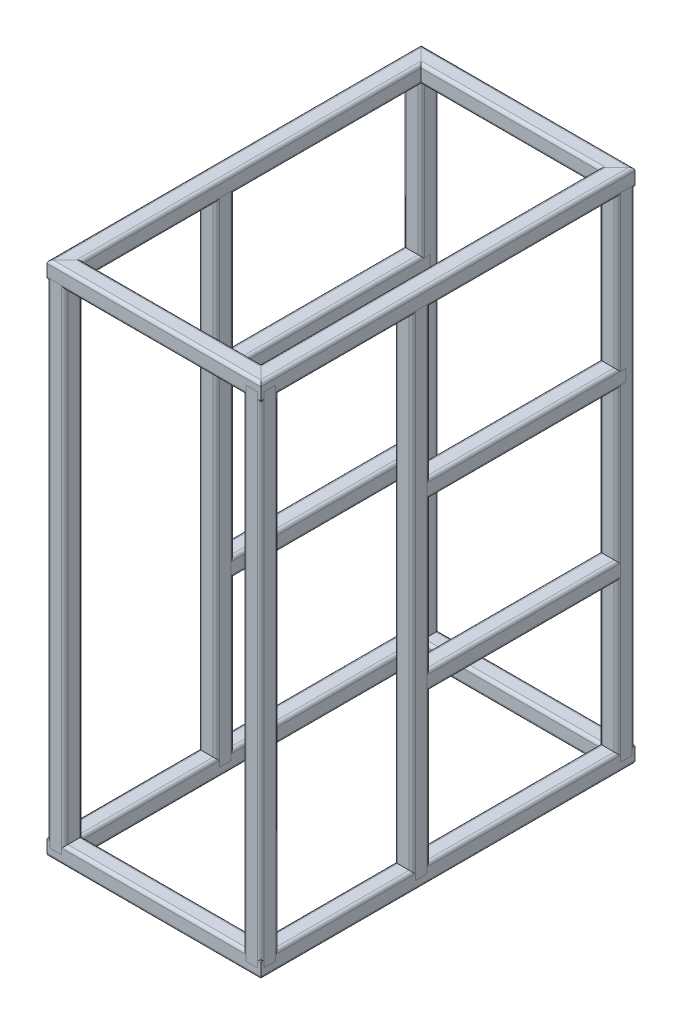
SolidWorks part; units mm, degrees
ref_plane "前视基准面" through (0, 0, 0) normal (0, 0, 1) x (1, 0, 0)
ref_plane "上视基准面" through (0, 0, 0) normal (0, 1, 0) x (1, 0, 0)
ref_plane "右视基准面" through (0, 0, 0) normal (1, 0, 0) x (0, 0, -1)
sketch "草图1" plane through (0, 0, 0) normal (0, 0, 1) x (1, 0, 0)
  line L1 (-165, -420) -> (165, -420)
  line L2 (-165, -420) -> (-165, 420)
  line L3 (-165, 420) -> (165, 420)
  line L4 (165, -420) -> (165, 420)
  line L5 (-165, -420) -> (165, 420) construction
  line L6 (-165, 420) -> (165, -420) construction
  point P0 (0, 0)
  dimension "D1" = 840
  dimension "D2" = 330
sketch3d "3D草图1"
  line L0 (165, 420, 0) -> (165, 420, -600)
  line L1 (165, 420, -600) -> (165, -420, -600)
  line L2 (165, -420, 0) -> (165, -420, -600)
  line L3 (-165, 420, 0) -> (-165, 420, -600)
  line L4 (-165, 420, -600) -> (165, 420, -600)
  line L5 (-165, 420, -600) -> (-165, -420, -600)
  line L6 (-165, -420, 0) -> (-165, -420, -600)
  line L7 (165, -420, -600) -> (-165, -420, -600)
  line L8 (165, -420, -255) -> (165, 420, -255)
  line L9 (-165, -420, -255) -> (-165, 420, -255)
  line L10 (165, -140, -255) -> (165, -140, -600)
  line L11 (165, 140, -255) -> (165, 140, -600)
  line L12 (-165, 140, -255) -> (-165, 140, -600)
  line L13 (-165, -140, -255) -> (-165, -140, -600)
  line L14 (165, -420, 0) -> (165, 420, 0) construction
  line L15 (-165, -420, 0) -> (-165, 420, 0) construction
  dimension "D1" = 280
  dimension "D2" = 280
  dimension "D3" = 255
  dimension "D4" = 280
  dimension "D5" = 280
  dimension "D6" = 255
  dimension "D7" = 600
other "方形管 30 X 30 X 2.6(1)"
ref_plane "基准面1" through (-165, -420, 0) normal (1, 0, 0) x (0, 1, 0)
sketch "Sketch1" plane through (-165, -420, 0) normal (1, 0, 0) x (0, 1, 0)
  line L0 (-9.8, -12.4) -> (9.8, -12.4)
  line L1 (-12.4, -9.8) -> (-12.4, 9.8)
  line L2 (9.8, 12.4) -> (-9.8, 12.4)
  line L3 (12.4, 9.8) -> (12.4, -9.8)
  line L4 (-9.8, -15) -> (9.8, -15)
  line L5 (-15, -9.8) -> (-15, 9.8)
  line L6 (9.8, 15) -> (-9.8, 15)
  line L7 (15, 9.8) -> (15, -9.8)
  arc A0 (15, 9.8) -> (9.8, 15) centre (9.8, 9.8) ccw
  arc A1 (9.8, -15) -> (15, -9.8) centre (9.8, -9.8) ccw
  arc A2 (-15, -9.8) -> (-9.8, -15) centre (-9.8, -9.8) ccw
  arc A3 (-9.8, 15) -> (-15, 9.8) centre (-9.8, 9.8) ccw
  arc A4 (-9.8, 12.4) -> (-12.4, 9.8) centre (-9.8, 9.8) ccw
  arc A5 (12.4, 9.8) -> (9.8, 12.4) centre (9.8, 9.8) ccw
  arc A6 (9.8, -12.4) -> (12.4, -9.8) centre (9.8, -9.8) ccw
  arc A7 (-12.4, -9.8) -> (-9.8, -12.4) centre (-9.8, -9.8) ccw
  point P0 (-15, 0)
  point P1 (15, 0)
  point P2 (0, 15)
  point P3 (0, -15)
  point P4 (0, 0)
  point P5 (-15, -15)
  point P6 (15, -15)
  point P7 (15, 15)
  point P8 (-15, 15)
  point P33 (0, 0)
  dimension "D1" = 5.2
  dimension "Thickness" = 2.6
  dimension "V_leg" = 30
other "方形管 30 X 30 X 2.6(2)"
ref_plane "基准面2" through (165, -420, 0) normal (0, 1, 0) x (-1, 0, 0)
sketch "Sketch11" plane through (165, -420, 0) normal (0, 1, 0) x (-1, 0, 0)
  line L0 (-9.8, -12.4) -> (9.8, -12.4)
  line L1 (-12.4, -9.8) -> (-12.4, 9.8)
  line L2 (9.8, 12.4) -> (-9.8, 12.4)
  line L3 (12.4, 9.8) -> (12.4, -9.8)
  line L4 (-9.8, -15) -> (9.8, -15)
  line L5 (-15, -9.8) -> (-15, 9.8)
  line L6 (9.8, 15) -> (-9.8, 15)
  line L7 (15, 9.8) -> (15, -9.8)
  arc A0 (15, 9.8) -> (9.8, 15) centre (9.8, 9.8) ccw
  arc A1 (9.8, -15) -> (15, -9.8) centre (9.8, -9.8) ccw
  arc A2 (-15, -9.8) -> (-9.8, -15) centre (-9.8, -9.8) ccw
  arc A3 (-9.8, 15) -> (-15, 9.8) centre (-9.8, 9.8) ccw
  arc A4 (-9.8, 12.4) -> (-12.4, 9.8) centre (-9.8, 9.8) ccw
  arc A5 (12.4, 9.8) -> (9.8, 12.4) centre (9.8, 9.8) ccw
  arc A6 (9.8, -12.4) -> (12.4, -9.8) centre (9.8, -9.8) ccw
  arc A7 (-12.4, -9.8) -> (-9.8, -12.4) centre (-9.8, -9.8) ccw
  point P0 (-15, 0)
  point P1 (15, 0)
  point P2 (0, 15)
  point P3 (0, -15)
  point P4 (0, 0)
  point P5 (-15, -15)
  point P6 (15, -15)
  point P7 (15, 15)
  point P8 (-15, 15)
  point P33 (0, 0)
  dimension "D1" = 5.2
  dimension "Thickness" = 2.6
  dimension "V_leg" = 30
other "方形管 30 X 30 X 2.6(4)"
ref_plane "基准面3" through (-165, 420, 0) normal (1, 0, 0) x (0, 1, 0)
sketch "Sketch12" plane through (-165, 420, 0) normal (1, 0, 0) x (0, 1, 0)
  line L0 (-9.8, -12.4) -> (9.8, -12.4)
  line L1 (-12.4, -9.8) -> (-12.4, 9.8)
  line L2 (9.8, 12.4) -> (-9.8, 12.4)
  line L3 (12.4, 9.8) -> (12.4, -9.8)
  line L4 (-9.8, -15) -> (9.8, -15)
  line L5 (-15, -9.8) -> (-15, 9.8)
  line L6 (9.8, 15) -> (-9.8, 15)
  line L7 (15, 9.8) -> (15, -9.8)
  arc A0 (15, 9.8) -> (9.8, 15) centre (9.8, 9.8) ccw
  arc A1 (9.8, -15) -> (15, -9.8) centre (9.8, -9.8) ccw
  arc A2 (-15, -9.8) -> (-9.8, -15) centre (-9.8, -9.8) ccw
  arc A3 (-9.8, 15) -> (-15, 9.8) centre (-9.8, 9.8) ccw
  arc A4 (-9.8, 12.4) -> (-12.4, 9.8) centre (-9.8, 9.8) ccw
  arc A5 (12.4, 9.8) -> (9.8, 12.4) centre (9.8, 9.8) ccw
  arc A6 (9.8, -12.4) -> (12.4, -9.8) centre (9.8, -9.8) ccw
  arc A7 (-12.4, -9.8) -> (-9.8, -12.4) centre (-9.8, -9.8) ccw
  point P0 (-15, 0)
  point P1 (15, 0)
  point P2 (0, 15)
  point P3 (0, -15)
  point P4 (0, 0)
  point P5 (-15, -15)
  point P6 (15, -15)
  point P7 (15, 15)
  point P8 (-15, 15)
  point P33 (0, 0)
  dimension "D1" = 5.2
  dimension "Thickness" = 2.6
  dimension "V_leg" = 30
other "方形管 30 X 30 X 2.6(5)"
ref_plane "基准面4" through (165, -420, -255) normal (0, 1, 0) x (1, 0, 0)
sketch "Sketch13" plane through (165, -420, -255) normal (0, 1, 0) x (1, 0, 0)
  line L0 (-9.8, -12.4) -> (9.8, -12.4)
  line L1 (-12.4, -9.8) -> (-12.4, 9.8)
  line L2 (9.8, 12.4) -> (-9.8, 12.4)
  line L3 (12.4, 9.8) -> (12.4, -9.8)
  line L4 (-9.8, -15) -> (9.8, -15)
  line L5 (-15, -9.8) -> (-15, 9.8)
  line L6 (9.8, 15) -> (-9.8, 15)
  line L7 (15, 9.8) -> (15, -9.8)
  arc A0 (15, 9.8) -> (9.8, 15) centre (9.8, 9.8) ccw
  arc A1 (9.8, -15) -> (15, -9.8) centre (9.8, -9.8) ccw
  arc A2 (-15, -9.8) -> (-9.8, -15) centre (-9.8, -9.8) ccw
  arc A3 (-9.8, 15) -> (-15, 9.8) centre (-9.8, 9.8) ccw
  arc A4 (-9.8, 12.4) -> (-12.4, 9.8) centre (-9.8, 9.8) ccw
  arc A5 (12.4, 9.8) -> (9.8, 12.4) centre (9.8, 9.8) ccw
  arc A6 (9.8, -12.4) -> (12.4, -9.8) centre (9.8, -9.8) ccw
  arc A7 (-12.4, -9.8) -> (-9.8, -12.4) centre (-9.8, -9.8) ccw
  point P0 (-15, 0)
  point P1 (15, 0)
  point P2 (0, 15)
  point P3 (0, -15)
  point P4 (0, 0)
  point P5 (-15, -15)
  point P6 (15, -15)
  point P7 (15, 15)
  point P8 (-15, 15)
  point P33 (0, 0)
  dimension "D1" = 5.2
  dimension "Thickness" = 2.6
  dimension "V_leg" = 30
other "方形管 30 X 30 X 2.6(6)"
ref_plane "基准面5" through (165, -140, -255) normal (0, 0, -1) x (1, 0, 0)
sketch "Sketch14" plane through (165, -140, -255) normal (0, 0, -1) x (1, 0, 0)
  line L0 (-9.8, -12.4) -> (9.8, -12.4)
  line L1 (-12.4, -9.8) -> (-12.4, 9.8)
  line L2 (9.8, 12.4) -> (-9.8, 12.4)
  line L3 (12.4, 9.8) -> (12.4, -9.8)
  line L4 (-9.8, -15) -> (9.8, -15)
  line L5 (-15, -9.8) -> (-15, 9.8)
  line L6 (9.8, 15) -> (-9.8, 15)
  line L7 (15, 9.8) -> (15, -9.8)
  arc A0 (15, 9.8) -> (9.8, 15) centre (9.8, 9.8) ccw
  arc A1 (9.8, -15) -> (15, -9.8) centre (9.8, -9.8) ccw
  arc A2 (-15, -9.8) -> (-9.8, -15) centre (-9.8, -9.8) ccw
  arc A3 (-9.8, 15) -> (-15, 9.8) centre (-9.8, 9.8) ccw
  arc A4 (-9.8, 12.4) -> (-12.4, 9.8) centre (-9.8, 9.8) ccw
  arc A5 (12.4, 9.8) -> (9.8, 12.4) centre (9.8, 9.8) ccw
  arc A6 (9.8, -12.4) -> (12.4, -9.8) centre (9.8, -9.8) ccw
  arc A7 (-12.4, -9.8) -> (-9.8, -12.4) centre (-9.8, -9.8) ccw
  point P0 (-15, 0)
  point P1 (15, 0)
  point P2 (0, 15)
  point P3 (0, -15)
  point P4 (0, 0)
  point P5 (-15, -15)
  point P6 (15, -15)
  point P7 (15, 15)
  point P8 (-15, 15)
  point P33 (0, 0)
  dimension "D1" = 5.2
  dimension "Thickness" = 2.6
  dimension "V_leg" = 30
